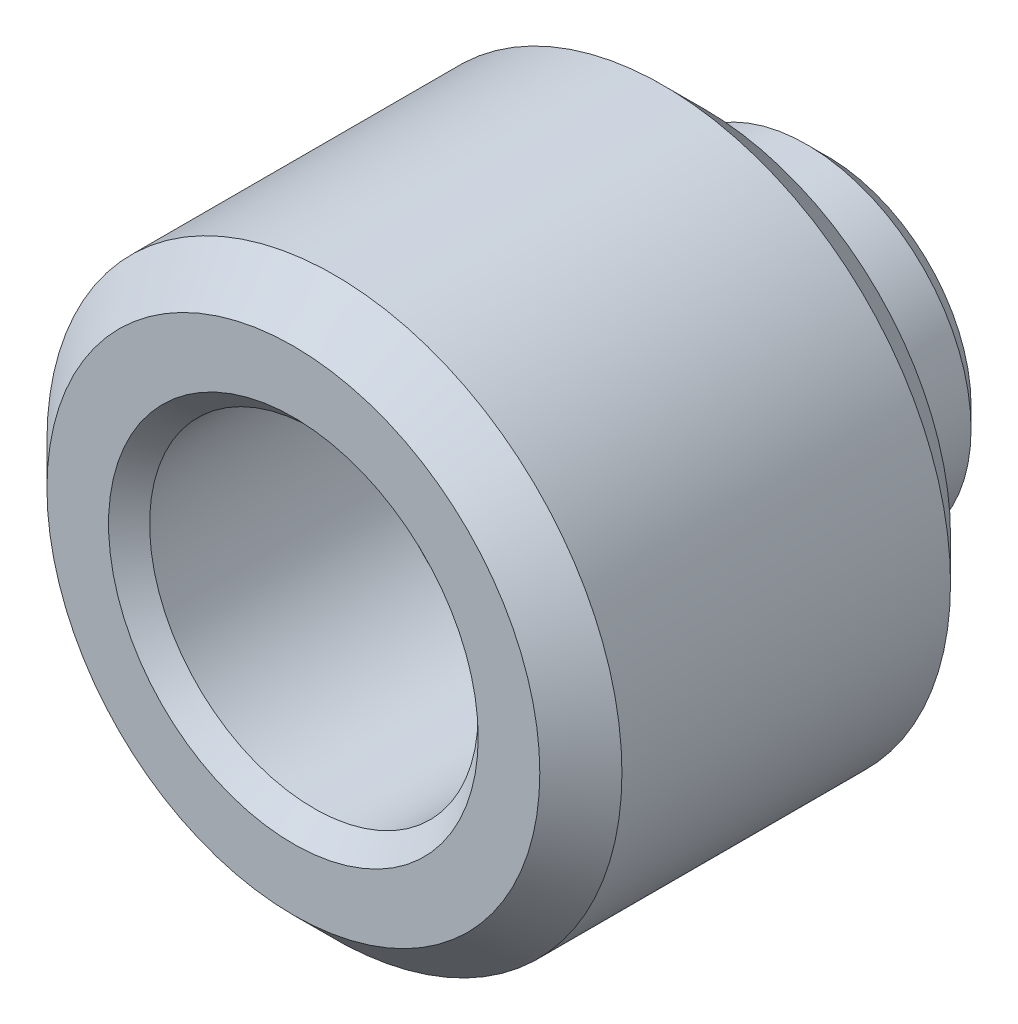
SolidWorks part; units mm, degrees
material "7075-T6 (SN)"
ref_plane "前视基准面" through (0, 0, 0) normal (0, 0, 1) x (1, 0, 0)
ref_plane "上视基准面" through (0, 0, 0) normal (0, 1, 0) x (1, 0, 0)
ref_plane "右视基准面" through (0, 0, 0) normal (1, 0, 0) x (0, 0, -1)
sketch "草图1" plane through (0, 0, 0) normal (0, 0, 1) x (1, 0, 0)
  circle A1 centre (0, -250) radius 32.5 construction
  circle A2 centre (42.8779, -281.1526) radius 7
  circle A5 centre (42.8779, -281.1526) radius 4
extrude "凸台-拉伸1" add sketch "草图1" along normal blind 10
sketch "草图2" plane through (0, 0, -3) normal (0, 0, 1) x (1, 0, 0)
  circle A0 centre (42.8779, -281.1526) radius 4 construction
  circle A1 centre (42.8779, -281.1526) radius 2.2 construction
  circle A2 centre (42.8779, -281.1526) radius 4
  circle A3 centre (42.8779, -281.1526) radius 2.2
extrude "凸台-拉伸2" add sketch "草图2" along normal blind 7
chamfer "倒角1" distance 1 angle 45 2 edges at (49.8779, -281.1526, 0) (49.8779, -281.1526, 10)
chamfer "倒角2" distance 0.5 angle 45 1 edges at (46.8779, -281.1526, -3)
chamfer "倒角3" distance 0.5 angle 45 1 edges at (46.8779, -281.1526, 10)
